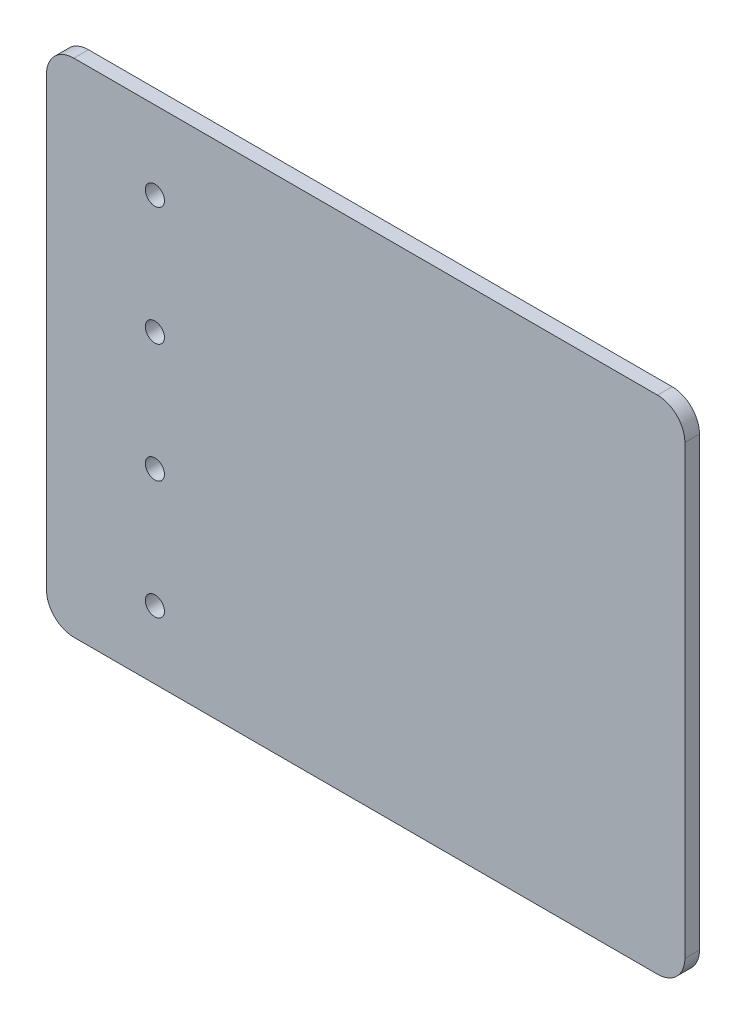
SolidWorks part; units mm, degrees
ref_plane "Plan de face" through (0, 0, 0) normal (0, 0, 1) x (1, 0, 0)
ref_plane "Plan de dessus" through (0, 0, 0) normal (0, 1, 0) x (1, 0, 0)
ref_plane "Plan de droite" through (0, 0, 0) normal (1, 0, 0) x (0, 0, -1)
sketch "Esquisse1" plane through (0, 0, 0) normal (0, 0, 1) x (1, 0, 0)
  line L1 (-35, -27.5) -> (35, -27.5)
  line L2 (-35, -27.5) -> (-35, 27.5)
  line L3 (-35, 27.5) -> (35, 27.5)
  line L4 (35, -27.5) -> (35, 27.5)
  line L5 (-35, -27.5) -> (35, 27.5) construction
  line L6 (-35, 27.5) -> (35, -27.5) construction
  point P0 (0, 0)
  dimension "D1" = 70
  dimension "D2" = 55
extrude "Boss.-Extru.1" add sketch "Esquisse1" along normal blind 1.6
fillet "Congé1" radius 3 4 edges at (-35, -27.5, 0.8) (35, -27.5, 0.8) (35, 27.5, 0.8) (-35, 27.5, 0.8)
sketch "Sketch1" plane through (0, 0, 0) normal (0, 0, -1) x (-1, 0, 0)
  circle A0 centre (23.118, -20.0667) radius 1.05
  circle A1 centre (23.118, -7.0667) radius 1.05
  circle A2 centre (23.118, 5.9333) radius 1.05
  circle A3 centre (23.118, 18.9333) radius 1.05
  dimension "D1" = 2.1
  dimension "D2" = 4
extrude "Cut-Extrude1" cut sketch "Sketch1" against normal through all
